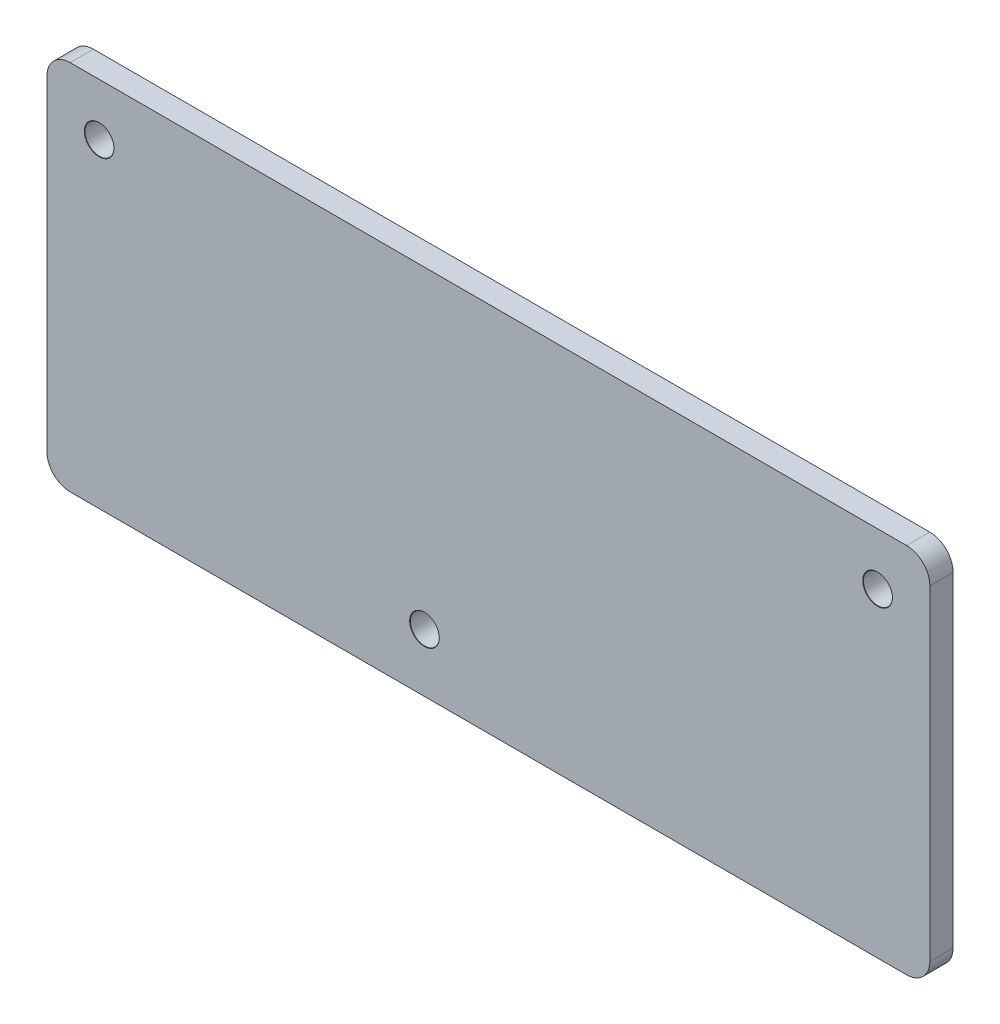
SolidWorks part; units mm, degrees
ref_plane "Front Plane" through (0, 0, 0) normal (0, 0, 1) x (1, 0, 0)
ref_plane "Top Plane" through (0, 0, 0) normal (0, 1, 0) x (1, 0, 0)
ref_plane "Right Plane" through (0, 0, 0) normal (1, 0, 0) x (0, 0, -1)
sketch "Model" plane through (0, 0, 0) normal (0, 0, 1) x (1, 0, 0)
  line L0 (-38, 14) -> (-38, -14)
  line L1 (-36, -16) -> (36, -16)
  line L2 (38, -14) -> (38, 14)
  line L3 (36, 16) -> (-36, 16)
  arc A0 (-36, 16) -> (-38, 14) centre (-36, 14) ccw
  arc A1 (-38, -14) -> (-36, -16) centre (-36, -14) ccw
  arc A2 (36, -16) -> (38, -14) centre (36, -14) ccw
  arc A3 (38, 14) -> (36, 16) centre (36, 14) ccw
extrude "Boss-Extrude1" add sketch "Model" along normal blind 2
sketch "Sketch2" plane through (0, 0, 2) normal (0, 0, 1) x (1, 0, 0)
  line L0 (36, 16) -> (-36, 16) construction
  line L1 (-38, 14) -> (-38, -14) construction
  line L2 (38, -14) -> (38, 14) construction
  line L3 (-36, -16) -> (36, -16) construction
  point P0 (-33.5, 11.5)
  point P1 (33.5, 11.5)
  point P2 (-5.5, -11)
  point P9 (0, 0)
  dimension "D1" = 4.5
  dimension "D2" = 4.5
  dimension "D3" = 4.5
  dimension "D4" = 5
  dimension "D5" = 32.5
hole_wizard "Tap Drill for M3 Tap1" positions "Sketch3" profile "Sketch4" hole size "M3" standard "ISO" end condition through all
sketch "Sketch3" plane through (0, 0, 2) normal (0, 0, 1) x (1, 0, 0)
  point P0 (-33.5, 11.5)
  point P3 (-5.5, -11)
  point P6 (33.5, 11.5)
sketch "Sketch4" plane through (-33.5, 11.5, 2) normal (1, 0, 0) x (0, -1, 0)
  line L0 (0, 0) -> (0, 2)
  line L1 (0, 2) -> (1.25, 2)
  line L2 (1.25, 2) -> (1.25, 0.025)
  line L3 (1.25, 0.025) -> (1.275, 0)
  line L5 (1.275, 0) -> (0, 0)
  line L6 (-1.25, 0.025) -> (-1.275, 0) construction
  line L11 (0, -6.35) -> (0, 107.95) construction
  dimension "Thru Hole Dia." = 2.5
  dimension "Thru Hole Depth" = 2
  dimension "Near C'Sink Dia." = 2.55
  dimension "Near C'Sink Angle" = 90
